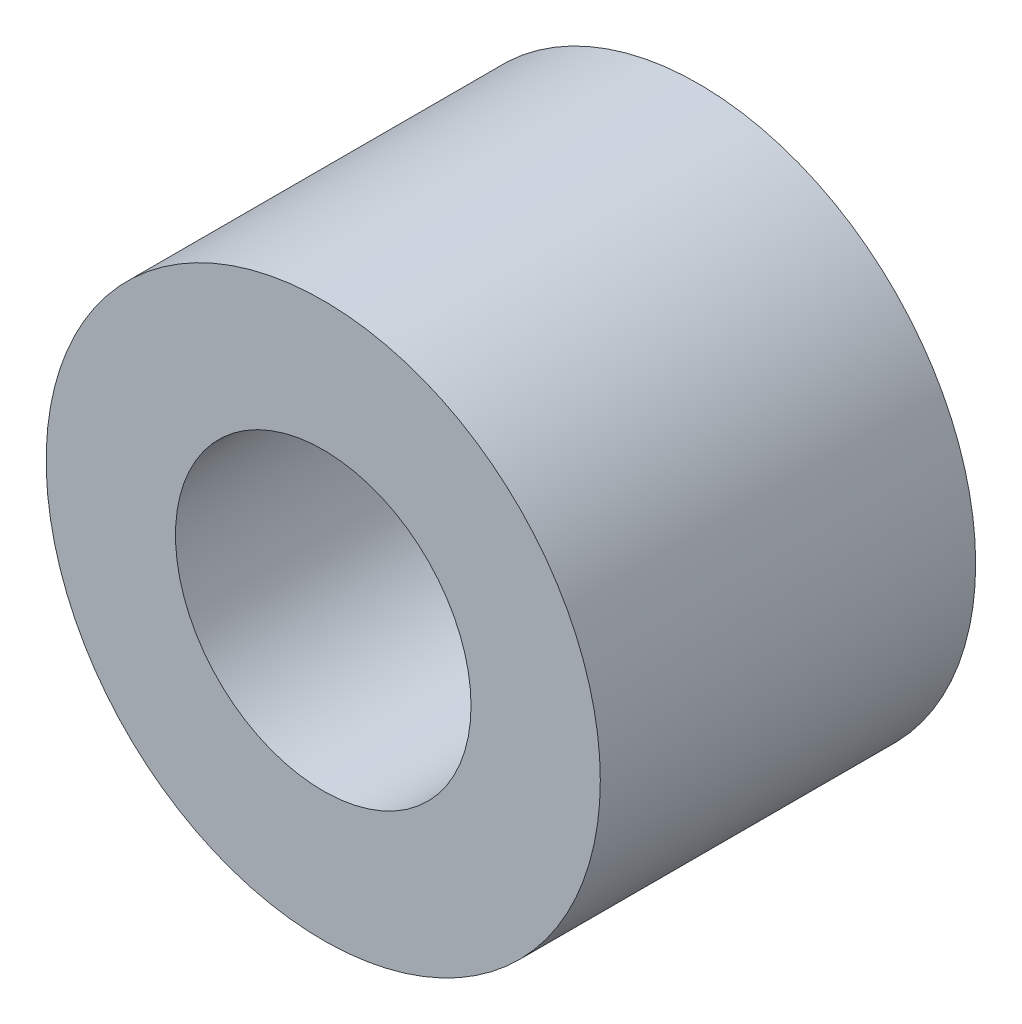
SolidWorks part; units mm, degrees
material "PET"
ref_plane "Front Plane" through (0, 0, 0) normal (0, 0, 1) x (1, 0, 0)
ref_plane "Top Plane" through (0, 0, 0) normal (0, 1, 0) x (1, 0, 0)
ref_plane "Right Plane" through (0, 0, 0) normal (1, 0, 0) x (0, 0, -1)
sketch "Sketch1" plane through (0, 0, 0) normal (0, 0, 1) x (1, 0, 0)
  circle A0 centre (0, 0) radius 2
  circle A1 centre (0, 0) radius 3.75
  dimension "D1" = 4
  dimension "D2" = 7.5
extrude "Boss-Extrude1" add sketch "Sketch1" along normal blind 5.08
